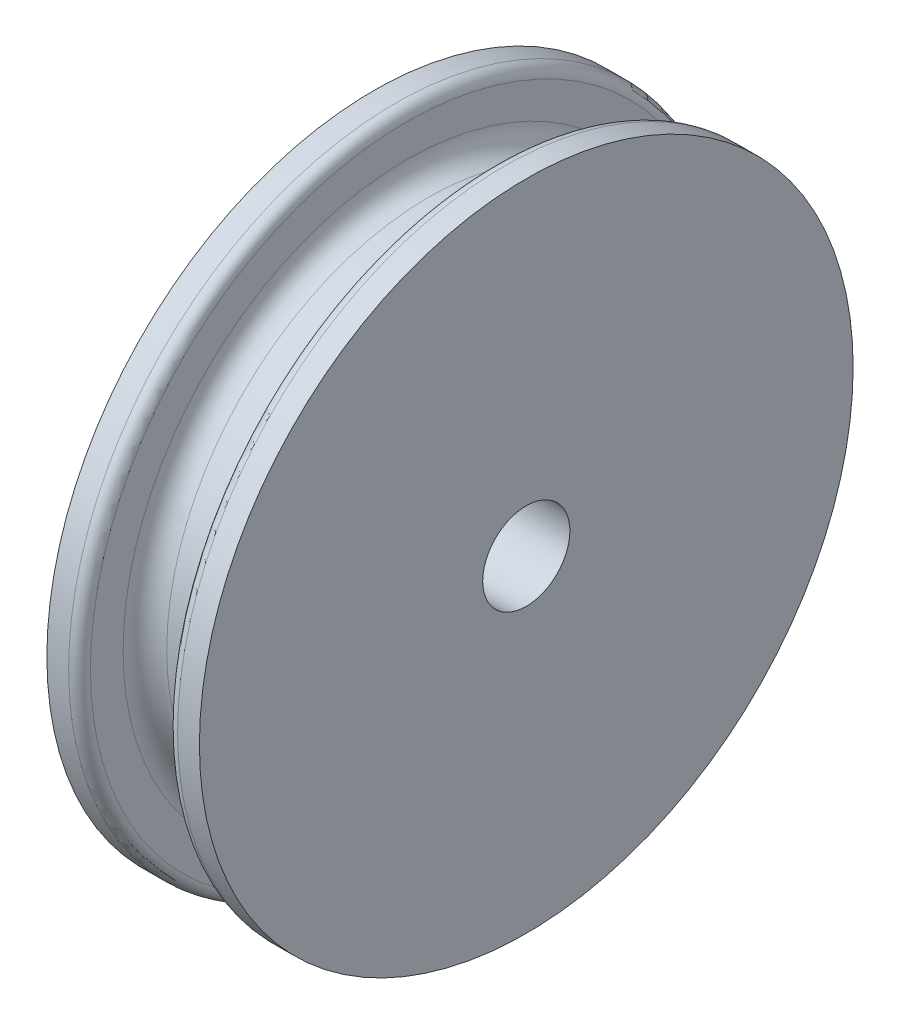
SolidWorks part; units mm, degrees
ref_plane "Front" through (0, 0, 0) normal (0, 0, 1) x (1, 0, 0)
ref_plane "Top" through (0, 0, 0) normal (0, 1, 0) x (1, 0, 0)
ref_plane "Right" through (0, 0, 0) normal (1, 0, 0) x (0, 0, -1)
sketch "Sketch1" plane through (0, 0, 0) normal (0, 0, 1) x (1, 0, 0)
  line L0 (-1.75, 1) -> (1.75, 1)
  line L1 (1.75, 1) -> (1.75, 7.5)
  line L2 (1.75, 7.5) -> (1, 7.5)
  line L3 (1, 7.5) -> (1, 6.5)
  line L4 (0.5, 6) -> (-0.5, 6)
  line L5 (0, 6) -> (0, 1) construction
  line L6 (0, 0) -> (4.984, 0) construction
  line L7 (-1, 7.5) -> (-1, 6.5)
  line L8 (-1.75, 7.5) -> (-1, 7.5)
  line L9 (-1.75, 1) -> (-1.75, 7.5)
  arc A0 (1, 6.5) -> (0.5, 6) centre (0.5, 6.5) cw
  arc A1 (-1, 6.5) -> (-0.5, 6) centre (-0.5, 6.5) ccw
  point P9 (0, 6)
  point P16 (1, 6)
  point P19 (-1, 6)
  dimension "D6" = 0.5
  dimension "D1" = 2
  dimension "D2" = 12
  dimension "D3" = 1.5
  dimension "D4" = 3.5
  dimension "D5" = 0.75
revolve "Revolve1" add sketch "Sketch1" angle 360 about L6
fillet "Fillet1" radius 0.25 2 edges at (-1, 0, 7.5) (1, 0, 7.5)
